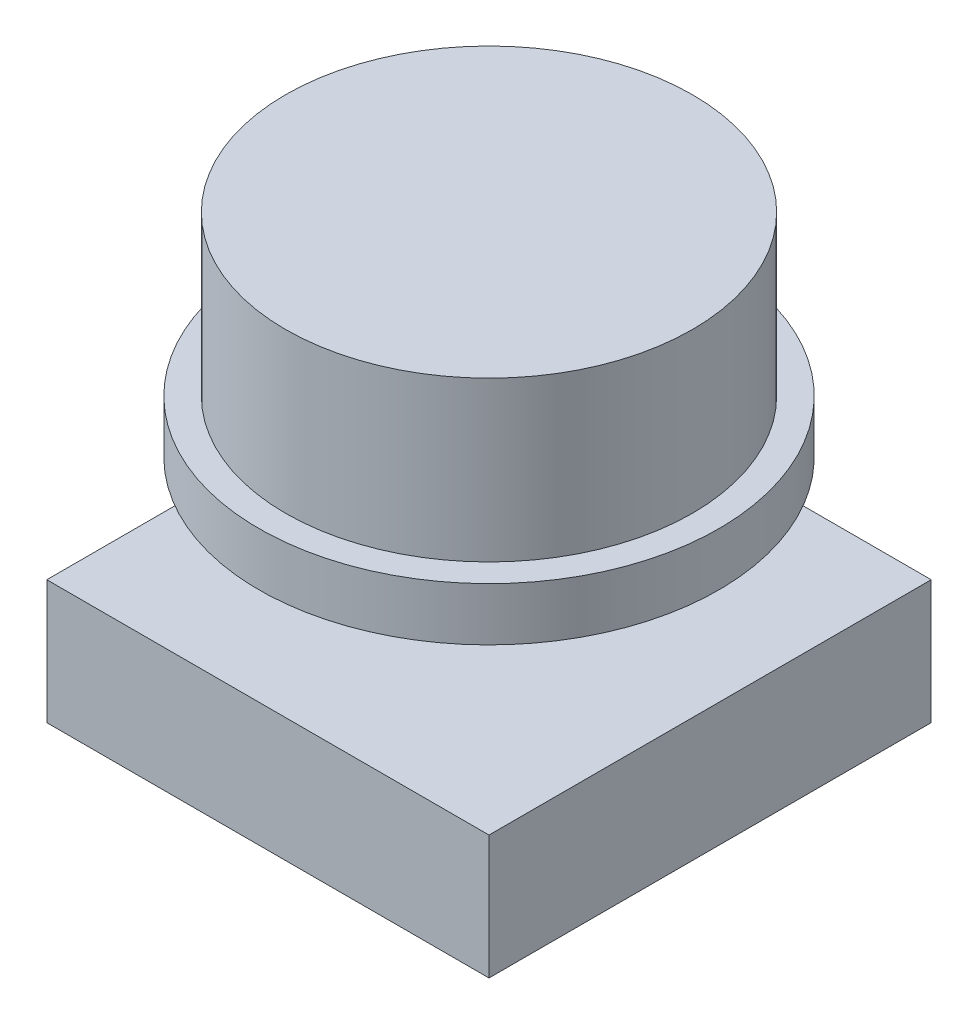
SolidWorks part; units mm, degrees
ref_plane "Спереди" through (0, 0, 0) normal (0, 0, 1) x (1, 0, 0)
ref_plane "Сверху" through (0, 0, 0) normal (0, 1, 0) x (1, 0, 0)
ref_plane "Справа" through (0, 0, 0) normal (1, 0, 0) x (0, 0, -1)
other "Configuration Table"
sketch "Эскиз1" plane through (0, 0, 0) normal (0, 1, 0) x (1, 0, 0)
  circle A0 centre (0, 0) radius 5.75
extrude "Бобышка-Вытянуть1" add sketch "Эскиз1" along normal blind 6
sketch "Эскиз2" plane through (0, 0, 0) normal (0, -1, 0) x (1, 0, 0)
  circle A0 centre (0, 0) radius 6.5
extrude "Бобышка-Вытянуть2" add sketch "Эскиз2" against normal blind 1.5
sketch "Эскиз3" plane through (0, 0, 0) normal (0, -1, 0) x (1, 0, 0)
  line L1 (-1.5, -1.5) -> (1.5, -1.5)
  line L2 (-1.5, -1.5) -> (-1.5, 1.5)
  line L3 (-1.5, 1.5) -> (1.5, 1.5)
  line L4 (1.5, -1.5) -> (1.5, 1.5)
  line L5 (-1.5, -1.5) -> (1.5, 1.5) construction
  line L6 (-1.5, 1.5) -> (1.5, -1.5) construction
  point P0 (0, 0)
  dimension "D1" = 3
extrude "Бобышка-Вытянуть3" add sketch "Эскиз3" along normal blind 12.5 from surface at -6 starting at face at (0, 6, 5.75)
sketch "Эскиз4" plane through (0, -6.5, 0) normal (0, -1, 0) x (1, 0, 0)
  line L1 (-6.25, -6.25) -> (6.25, -6.25)
  line L2 (-6.25, -6.25) -> (-6.25, 6.25)
  line L3 (-6.25, 6.25) -> (6.25, 6.25)
  line L4 (6.25, -6.25) -> (6.25, 6.25)
  line L5 (-6.25, -6.25) -> (6.25, 6.25) construction
  line L6 (-6.25, 6.25) -> (6.25, -6.25) construction
  point P0 (0, 0)
  dimension "D1" = 12.5
extrude "Бобышка-Вытянуть4" add sketch "Эскиз4" against normal blind 3.5
